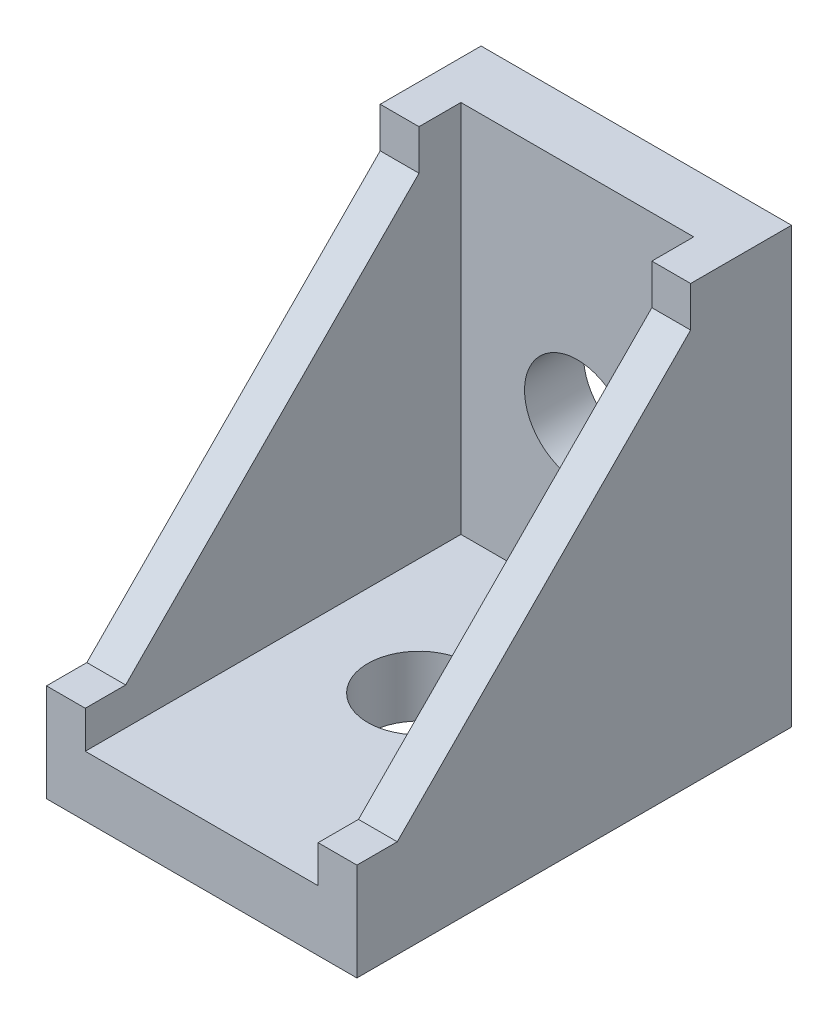
SolidWorks part; units mm, degrees
ref_plane "Front Plane" through (0, 0, 0) normal (0, 0, 1) x (1, 0, 0)
ref_plane "Top Plane" through (0, 0, 0) normal (0, 1, 0) x (1, 0, 0)
ref_plane "Right Plane" through (0, 0, 0) normal (1, 0, 0) x (0, 0, -1)
sketch "Sketch1" plane through (0, 0, 0) normal (0, 0, 1) x (1, 0, 0)
  line L1 (-10, 14) -> (10, 14)
  line L2 (-10, 14) -> (-10, -14)
  line L3 (-10, -14) -> (10, -14)
  line L4 (10, 14) -> (10, -14)
  line L5 (-10, 14) -> (10, -14) construction
  line L6 (-10, -14) -> (10, 14) construction
  circle A0 centre (0, 0) radius 3.4
  point P0 (0, 0)
  dimension "D3" = 6.8
  dimension "D1" = 20
  dimension "D2" = 28
extrude "Boss-Extrude1" add sketch "Sketch1" along normal blind 3.8
sketch "Sketch2" plane through (0, -14, 0) normal (0, -1, 0) x (1, 0, 0)
  line L1 (10, 0) -> (-10, 0)
  line L2 (10, 0) -> (10, 28)
  line L3 (10, 28) -> (-10, 28)
  line L4 (-10, 0) -> (-10, 28)
  circle A0 centre (0, 14) radius 3.3
  dimension "D3" = 6.6
  dimension "D1" = 20
  dimension "D2" = 28
  dimension "D4" = 14
extrude "Boss-Extrude2" add sketch "Sketch2" against normal blind 3.9
sketch "Sketch3" plane through (-10, 0, 0) normal (-1, 0, 0) x (0, 0, 1)
  line L0 (28, -10.1) -> (3.8, -10.1) construction
  line L1 (0, 14) -> (6.5, 14)
  line L2 (0, 14) -> (0, -10.1)
  line L3 (0, -10.1) -> (6.5, -10.1)
  line L4 (6.5, 14) -> (6.5, -10.1)
  dimension "D1" = 6.5
extrude "Boss-Extrude3" add sketch "Sketch3" against normal blind 2.5
mirror "Mirror1" about plane through (0, 0, 0) normal (1, 0, 0) of "Boss-Extrude3"
sketch "Sketch4" plane through (-10, 0, 0) normal (-1, 0, 0) x (0, 0, 1)
  line L0 (0, 14) -> (0, -14) construction
  line L1 (28, -14) -> (0, -14)
  line L2 (28, -14) -> (28, -7.7)
  line L3 (28, -7.7) -> (0, -7.7)
  line L4 (0, -14) -> (0, -7.7)
  dimension "D1" = 6.3
extrude "Boss-Extrude4" add sketch "Sketch4" against normal blind 2.5
mirror "Mirror2" about plane through (0, 0, 0) normal (1, 0, 0) of "Boss-Extrude4"
sketch "Sketch5" plane through (-10, 0, 0) normal (-1, 0, 0) x (0, 0, 1)
  line L0 (6.5, 11.4) -> (25.4, -7.7)
  line L1 (6.5, -7.7) -> (6.5, 14) construction
  line L2 (28, -7.7) -> (6.5, -7.7) construction
  line L3 (25.4, -7.7) -> (6.5, -7.7)
  line L4 (6.5, -7.7) -> (6.5, 11.4)
  dimension "D1" = 2.6
  dimension "D2" = 2.6
extrude "Boss-Extrude5" add sketch "Sketch5" against normal blind 2.5
mirror "Mirror3" about plane through (0, 0, 0) normal (1, 0, 0) of "Boss-Extrude5"
